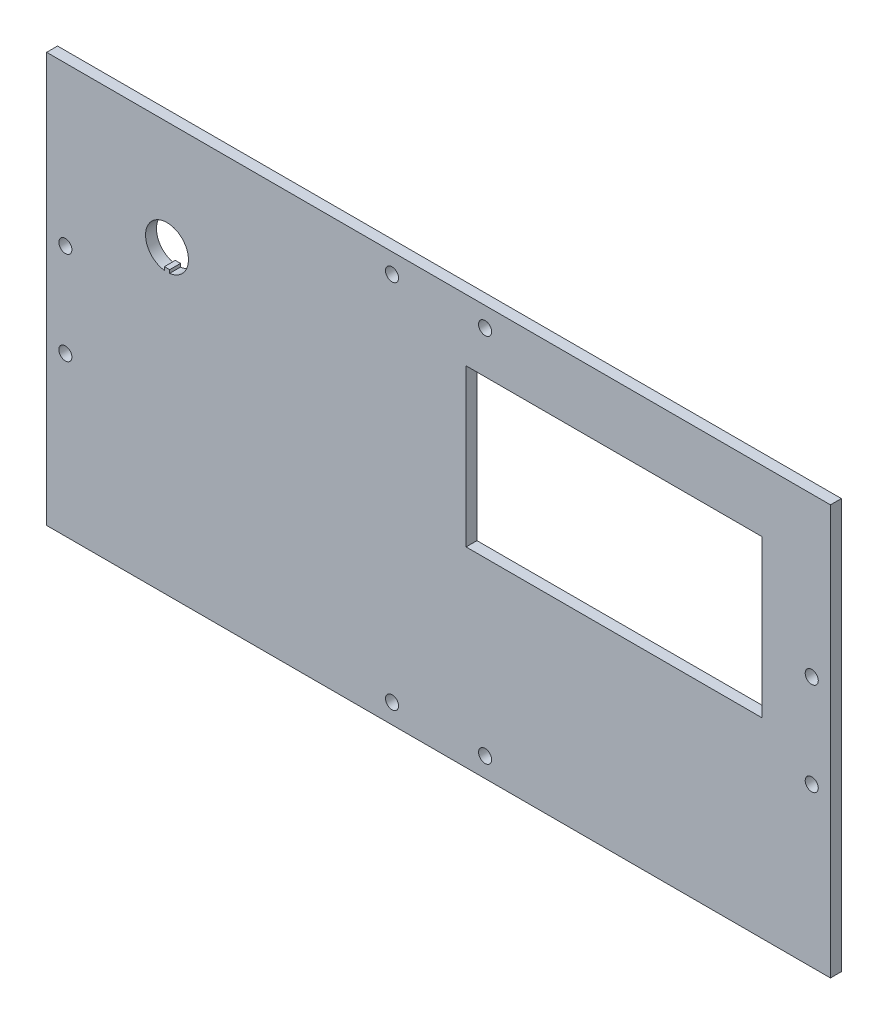
SolidWorks part; units mm, degrees
material "6061-T6 (SS)"
ref_plane "Front Plane" through (0, 0, 0) normal (0, 0, 1) x (1, 0, 0)
ref_plane "Top Plane" through (0, 0, 0) normal (0, 1, 0) x (1, 0, 0)
ref_plane "Right Plane" through (0, 0, 0) normal (1, 0, 0) x (0, 0, -1)
sketch "Sketch1" plane through (0, 0, 0) normal (0, 0, 1) x (1, 0, 0)
  line L0 (-108.7209, 13.5509) -> (-108.7209, -13.5509) construction
  line L1 (-114.173, -59.69) -> (114.173, -59.69)
  line L2 (-114.173, -59.69) -> (-114.173, 59.69)
  line L3 (-114.173, 59.69) -> (114.173, 59.69)
  line L4 (114.173, -59.69) -> (114.173, 59.69)
  line L5 (-114.173, -59.69) -> (114.173, 59.69) construction
  line L6 (-114.173, 59.69) -> (114.173, -59.69) construction
  line L7 (-108.7209, 0) -> (-114.173, 0) construction
  line L8 (0, 0) -> (0, 59.69) construction
  line L9 (-79.873, 21.8121) -> (-79.873, 22.756)
  line L10 (8.023, 41.69) -> (94.173, 41.69)
  line L11 (8.023, 41.69) -> (8.023, -4.01)
  line L12 (8.023, -4.01) -> (94.173, -4.01)
  line L13 (94.173, 41.69) -> (94.173, -4.01)
  line L14 (-79.873, 22.756) -> (-78.349, 22.756)
  line L15 (-78.349, 22.756) -> (-78.349, 21.8121)
  line L16 (-79.111, 22.756) -> (-79.111, 34.2622) construction
  line L17 (-56.515, 32.8) -> (-56.515, 23.2277) construction
  line L18 (-29.591, 32.8) -> (-29.591, 23.2277) construction
  line L19 (-43.053, -39.7921) -> (-43.053, 11.0079) construction
  line L20 (-101.473, 11.0079) -> (15.367, 11.0079) construction
  line L21 (-101.473, 11.0079) -> (-101.473, -39.7921) construction
  line L22 (-101.473, -39.7921) -> (15.367, -39.7921) construction
  line L23 (15.367, 11.0079) -> (15.367, -39.7921) construction
  line L24 (-18.923, -39.7921) -> (-7.493, -39.7921) construction
  line L25 (-18.923, -39.7921) -> (-18.923, -51.2221) construction
  line L26 (-18.923, -51.2221) -> (-7.493, -51.2221) construction
  line L27 (-7.493, -39.7921) -> (-7.493, -51.2221) construction
  line L28 (-18.923, 11.0079) -> (-7.493, 11.0079) construction
  line L29 (-18.923, 11.0079) -> (-18.923, 22.4379) construction
  line L30 (-18.923, 22.4379) -> (-7.493, 22.4379) construction
  line L31 (-7.493, 11.0079) -> (-7.493, 22.4379) construction
  line L32 (-78.613, -39.7921) -> (-78.613, -51.2221) construction
  line L33 (-67.183, -51.2221) -> (-78.613, -51.2221) construction
  line L34 (-67.183, -39.7921) -> (-67.183, -51.2221) construction
  line L35 (-67.183, -39.7921) -> (-78.613, -39.7921) construction
  line L36 (-78.613, 11.0079) -> (-78.613, 22.4379) construction
  line L37 (-67.183, 22.4379) -> (-78.613, 22.4379) construction
  line L38 (-67.183, 11.0079) -> (-67.183, 22.4379) construction
  line L39 (-67.183, 11.0079) -> (-78.613, 11.0079) construction
  line L40 (-72.898, -51.2221) -> (-72.898, -46.0171) construction
  line L41 (-72.898, -46.0171) -> (-12.898, -46.0171) construction
  line L42 (-72.898, -46.0171) -> (-72.898, 17.2329) construction
  line L43 (-72.898, 17.2329) -> (-12.898, 17.2329) construction
  line L44 (-12.898, -46.0171) -> (-12.898, 17.2329) construction
  line L45 (-101.473, -14.3921) -> (-72.898, -14.3921) construction
  line L46 (-13.5509, 53.975) -> (13.5509, 53.975) construction
  line L47 (0, 53.975) -> (0, 59.69) construction
  circle A0 centre (-108.7209, 13.5509) radius 1.905
  circle A1 centre (-108.7209, -13.5509) radius 1.905
  circle A2 centre (108.7209, -13.5509) radius 1.905
  circle A3 centre (108.7209, 13.5509) radius 1.905
  circle A4 centre (-43.053, 28.0138) radius 14.2875 construction
  circle A5 centre (-79.111, 28.0138) radius 6.2484
  circle A6 centre (-12.898, 17.2329) radius 1.905 construction
  circle A7 centre (-12.898, -46.0171) radius 1.905 construction
  circle A8 centre (-72.898, -46.0171) radius 1.905 construction
  circle A9 centre (-72.898, 17.2329) radius 1.905 construction
  circle A10 centre (-13.5509, 53.975) radius 1.905
  circle A11 centre (13.5509, 53.975) radius 1.905
  circle A12 centre (13.5509, -53.975) radius 1.905
  circle A13 centre (-13.5509, -53.975) radius 1.905
  point P0 (0, 0)
  point P34 (-56.515, 28.0138)
  point P72 (-79.111, 28.0138)
  dimension "D3" = 3.81
  dimension "D6" = 28.575
  dimension "D9" = 12.4968
  dimension "D25" = 3.81
  dimension "D1" = 228.346
  dimension "D2" = 119.38
  dimension "D4" = 108.7209
  dimension "D5" = 27.1018
  dimension "D7" = 86.15
  dimension "D8" = 45.7
  dimension "D10" = 1.524
  dimension "D11" = 11.5062
  dimension "D12" = 26.924
  dimension "D13" = 13.462
  dimension "D14" = 50.8
  dimension "D15" = 116.84
  dimension "D16" = 73.66
  dimension "D17" = 22.86
  dimension "D18" = 11.43
  dimension "D22" = 20
  dimension "D23" = 12.7
  dimension "D26" = 63.25
  dimension "D27" = 60
  dimension "D28" = 5.715
  dimension "D29" = 18
extrude "Boss-Extrude1" add sketch "Sketch1" along normal blind 3.175 contours L1 L4 L3 L2 A12 A11 A10 A9 A8 A7 A6 A5 A4 A2 A1 A0 L10 L13 L12 L11 A3 A13 | L9 A5 L15 L14 | L17 A4 | L18 A4
sketch "Sketch2" plane through (0, 0, 3.175) normal (0, 0, 1) x (1, 0, 0)
  line L0 (79.273, -24.83) -> (98.273, -48.83) construction
  circle A0 centre (88.773, -36.83) radius 12
  circle A1 centre (79.273, -24.83) radius 1.55
  circle A2 centre (98.273, -48.83) radius 1.55
  point P7 (88.773, -36.83)
  dimension "D3" = 3.1
  dimension "D4" = 24
  dimension "D1" = 19
  dimension "D2" = 24
  dimension "D5" = 25.4
  dimension "D6" = 22.86
extrude "Cut-Extrude1" [suppressed] cut sketch "Sketch2" against normal through all
sketch "Sketch3" plane through (0, 0, 3.175) normal (0, 0, 1) x (1, 0, 0)
  line L0 (-29.591, 32.8) -> (-29.591, 23.2277) construction
  line L1 (-56.515, 32.8) -> (-56.515, 23.2277) construction
  line L2 (-29.591, 32.8) -> (-29.591, 23.2277)
  line L3 (-56.515, 32.8) -> (-56.515, 23.2277)
  circle A0 centre (-43.053, 28.0138) radius 14.2875 construction
  circle A1 centre (-43.053, 28.0138) radius 14.2875
extrude "Cut-Extrude2" [suppressed] cut sketch "Sketch3" against normal through all contours L2 A1 L3
